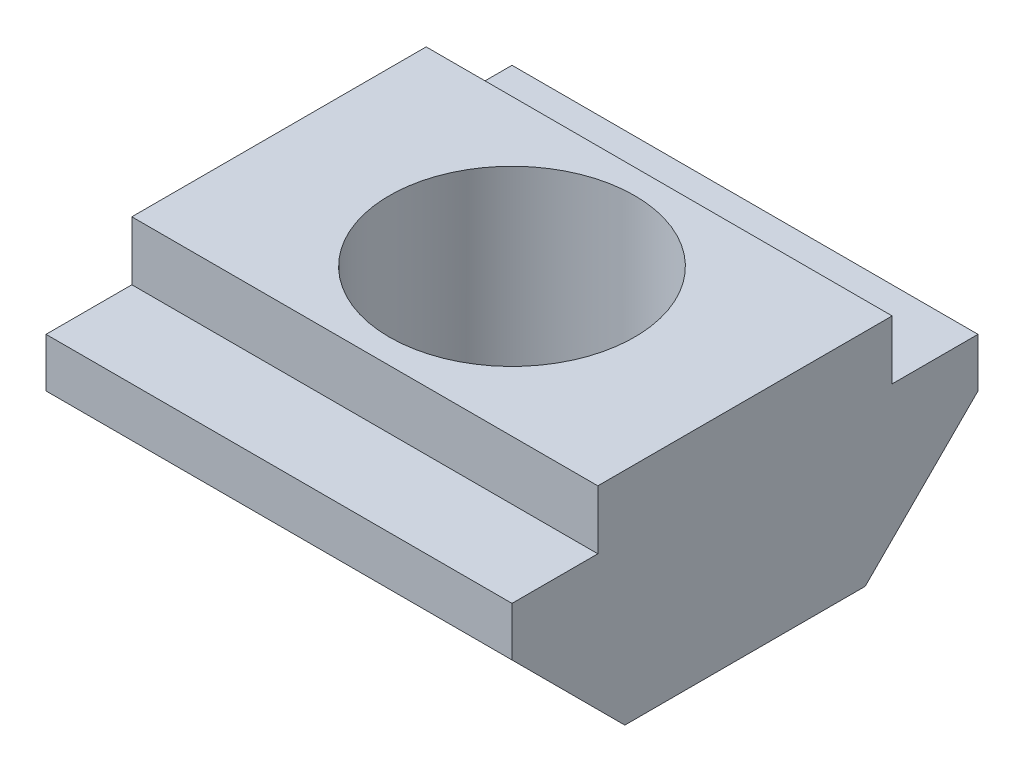
SolidWorks part; units mm, degrees
ref_plane "前视基准面" through (0, 0, 0) normal (0, 0, 1) x (1, 0, 0)
ref_plane "上视基准面" through (0, 0, 0) normal (0, 1, 0) x (1, 0, 0)
ref_plane "右视基准面" through (0, 0, 0) normal (1, 0, 0) x (0, 0, -1)
sketch "草图1" plane through (0, 0, 0) normal (0, 1, 0) x (1, 0, 0)
  line L0 (0, 0) -> (9.5, 0)
  line L1 (9.5, 0) -> (9.5, 9.5)
  line L2 (9.5, 9.5) -> (0, 9.5)
  line L3 (0, 9.5) -> (0, 0)
  dimension "D1" = 9.5
  dimension "D2" = 9.5
extrude "凸台-拉伸1" add sketch "草图1" along normal blind 3.3
sketch "草图2" plane through (0, 3.3, 0) normal (0, 1, 0) x (1, 0, 0)
  line L0 (0, 1.75) -> (9.5, 1.75)
  line L1 (0, 9.5) -> (0, 0) construction
  line L2 (9.5, 0) -> (9.5, 9.5) construction
  line L3 (9.5, 7.75) -> (0, 7.75)
  line L8 (0, 9.5) -> (0, 0)
  line L9 (0, 0) -> (9.5, 0)
  line L10 (9.5, 0) -> (9.5, 9.5)
  line L11 (9.5, 9.5) -> (0, 9.5)
  line L12 (0, 7.75) -> (0, 1.75)
  line L14 (9.5, 1.75) -> (9.5, 7.75)
  dimension "D2" = 1.75
  dimension "D3" = 6
  dimension "D1" = 0
extrude "凸台-拉伸2" add sketch "草图2" along normal blind 1.2
sketch "草图3" plane through (0, 4.5, 0) normal (0, 1, 0) x (1, 0, 0)
  line L0 (0, 7.75) -> (0, 1.75) construction
  line L1 (9.5, 9.5) -> (0, 9.5) construction
  circle A0 centre (4.75, 4.75) radius 2.5
  dimension "D1" = 5
  dimension "D2" = 4.75
  dimension "D3" = 4.75
extrude "切除-拉伸1" cut sketch "草图3" against normal through all
sketch "草图4" plane through (0, 0, 0) normal (-1, 0, 0) x (0, 0, 1)
  line L0 (-9.5, 2.3) -> (-7.2, 0)
  line L1 (0, 2.3) -> (-2.3, 0)
  line L2 (-2.3, 0) -> (0, 0)
  line L8 (-9.5, 0) -> (0, 0)
  line L9 (0, 0) -> (0, 3.3)
  line L10 (0, 3.3) -> (-1.75, 3.3)
  line L11 (-1.75, 3.3) -> (-1.75, 4.5)
  line L12 (-1.75, 4.5) -> (-7.75, 4.5)
  line L13 (-7.75, 4.5) -> (-7.75, 3.3)
  line L14 (-7.75, 3.3) -> (-9.5, 3.3)
  line L15 (-9.5, 3.3) -> (-9.5, 0)
  line L16 (-9.5, 0) -> (-7.2, 0)
  line L17 (0, 0) -> (0, 2.3)
  line L23 (-9.5, 2.3) -> (-9.5, 0)
  dimension "D2" = 1
  dimension "D3" = 1
  dimension "D4" = 45
  dimension "D5" = 45
  dimension "D1" = 0
extrude "切除-拉伸2" cut sketch "草图4" against normal through all
